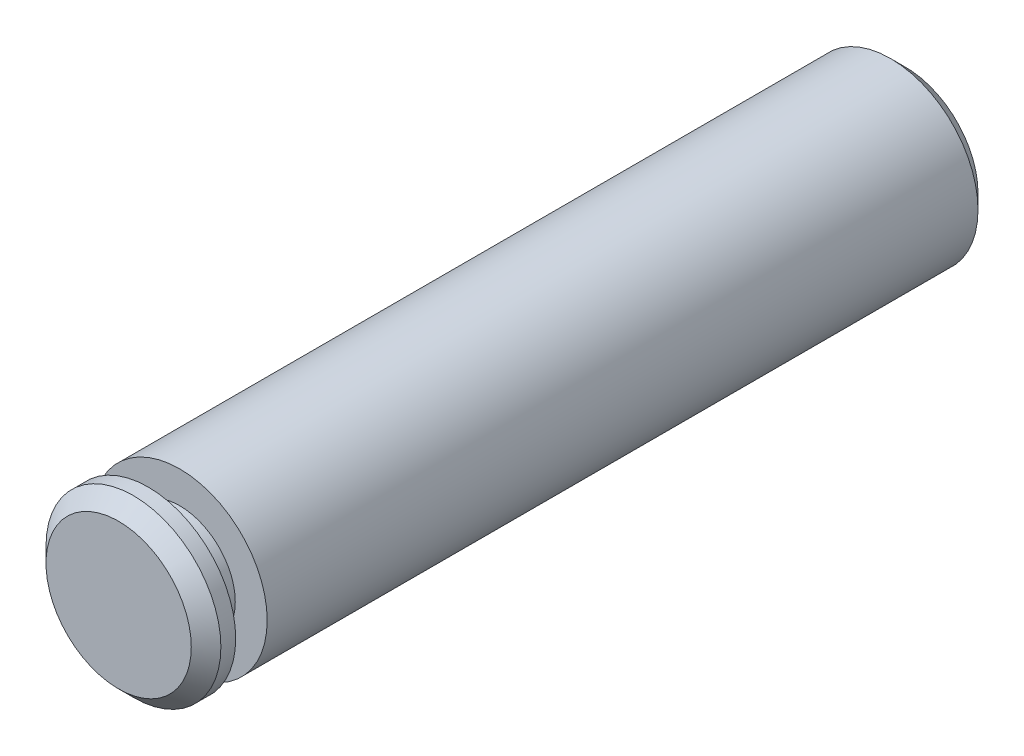
SolidWorks part; units mm, degrees
material "AISI Type A2 Tool Steel"
ref_plane "Front Plane" through (0, 0, 0) normal (0, 0, 1) x (1, 0, 0)
ref_plane "Top Plane" through (0, 0, 0) normal (0, 1, 0) x (1, 0, 0)
ref_plane "Right Plane" through (0, 0, 0) normal (1, 0, 0) x (0, 0, -1)
sketch "Sketch1" plane through (0, 0, 0) normal (0, 0, 1) x (1, 0, 0)
  circle A0 centre (0, 0) radius 1.4999
  dimension "D1" = 2.9997
extrude "Boss-Extrude1" add sketch "Sketch1" along normal mid plane 13.4937
sketch "Sketch2" plane through (0, 0, 0) normal (1, 0, 0) x (0, 0, -1)
  line L0 (-6.7469, -1.4999) -> (6.7469, -1.4999) construction
  line L1 (-6.2389, -1.4999) -> (-5.6989, -1.4999)
  line L2 (-6.2389, -1.4999) -> (-6.2389, -0.9525)
  line L3 (-6.2389, -0.9525) -> (-5.6989, -0.9525)
  line L4 (-5.6989, -1.4999) -> (-5.6989, -0.9525)
  line L5 (-6.7469, 1.4999) -> (-6.7469, -1.4999) construction
  line L6 (-8.828, 0) -> (8.9454, 0) construction
  line L7 (1.6485, 0) -> (-1.6485, 0) construction
  line L8 (0, 2.428) -> (0, -3.7184) construction
  dimension "D1" = 0.508
  dimension "D2" = 0.54
  dimension "D3" = 1.905
revolve "Cut-Revolve1" cut sketch "Sketch2" angle 360 about L6
chamfer "Chamfer1" distance 0.254 angle 45
